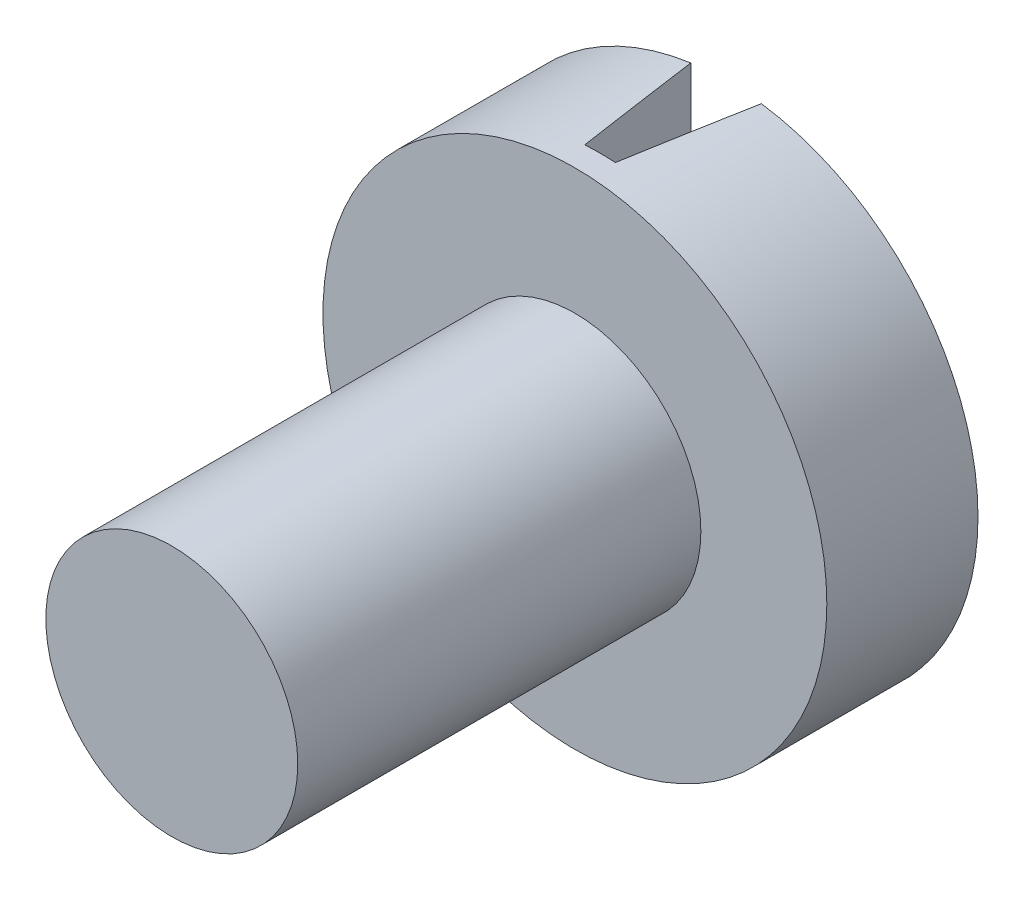
SolidWorks part; units mm, degrees
ref_plane "Alzado" through (0, 0, 0) normal (0, 0, 1) x (1, 0, 0)
ref_plane "Planta" through (0, 0, 0) normal (0, 1, 0) x (1, 0, 0)
ref_plane "Vista lateral" through (0, 0, 0) normal (1, 0, 0) x (0, 0, -1)
sketch "Croquis1" plane through (0, 0, 0) normal (0, 0, 1) x (1, 0, 0)
  circle A0 centre (0, 0) radius 2.5
  dimension "D1" = 5
extrude "Saliente-Extruir1" add sketch "Croquis1" along normal blind 8
sketch "Croquis2" plane through (0, 0, 0) normal (0, 0, 1) x (1, 0, 0)
  circle A0 centre (0, 0) radius 5
  dimension "D1" = 10
extrude "Saliente-Extruir2" add sketch "Croquis2" against normal blind 3
sketch "Croquis3" plane through (0, 0, -3) normal (0, 0, -1) x (-1, 0, 0)
  line L0 (0, 5) -> (0, -5) construction
  line L2 (-0.7, -5.5) -> (0.7, -5.5)
  line L3 (-0.7, -5.5) -> (-0.7, 5.5)
  line L4 (-0.7, 5.5) -> (0.7, 5.5)
  line L5 (0.7, -5.5) -> (0.7, 5.5)
  line L6 (-0.7, -5.5) -> (0.7, 5.5) construction
  line L7 (-0.7, 5.5) -> (0.7, -5.5) construction
  circle A0 centre (0, 0) radius 5 construction
  point P5 (0, 0)
  dimension "D1" = 1.4
  dimension "D2" = 11
extrude "Cortar-Extruir2" cut sketch "Croquis3" against normal blind 2.5 draft 9
